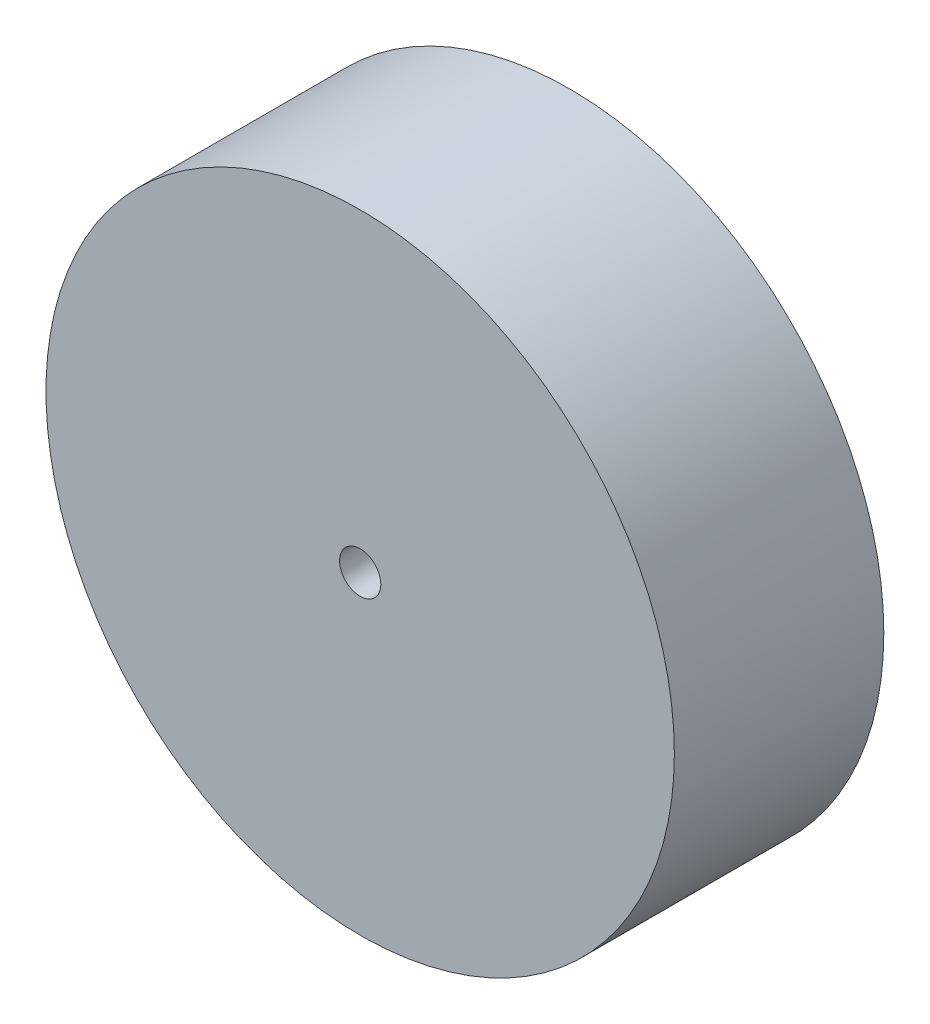
SolidWorks part; units mm, degrees
material "Hexcel AS4C (3000 Filaments)"
ref_plane "Front Plane" through (0, 0, 0) normal (0, 0, 1) x (1, 0, 0)
ref_plane "Top Plane" through (0, 0, 0) normal (0, 1, 0) x (1, 0, 0)
ref_plane "Right Plane" through (0, 0, 0) normal (1, 0, 0) x (0, 0, -1)
sketch "Sketch1" plane through (0, 0, 0) normal (0, 0, 1) x (1, 0, 0)
  circle A0 centre (0, 0) radius 38.1
extrude "Extrude1" add sketch "Sketch1" along normal blind 25.4
sketch "Sketch2" plane through (0, 0, 25.4) normal (0, 0, 1) x (1, 0, 0)
  circle A0 centre (0, 0) radius 2.5
extrude "Extrude2" cut sketch "Sketch2" against normal blind 15
